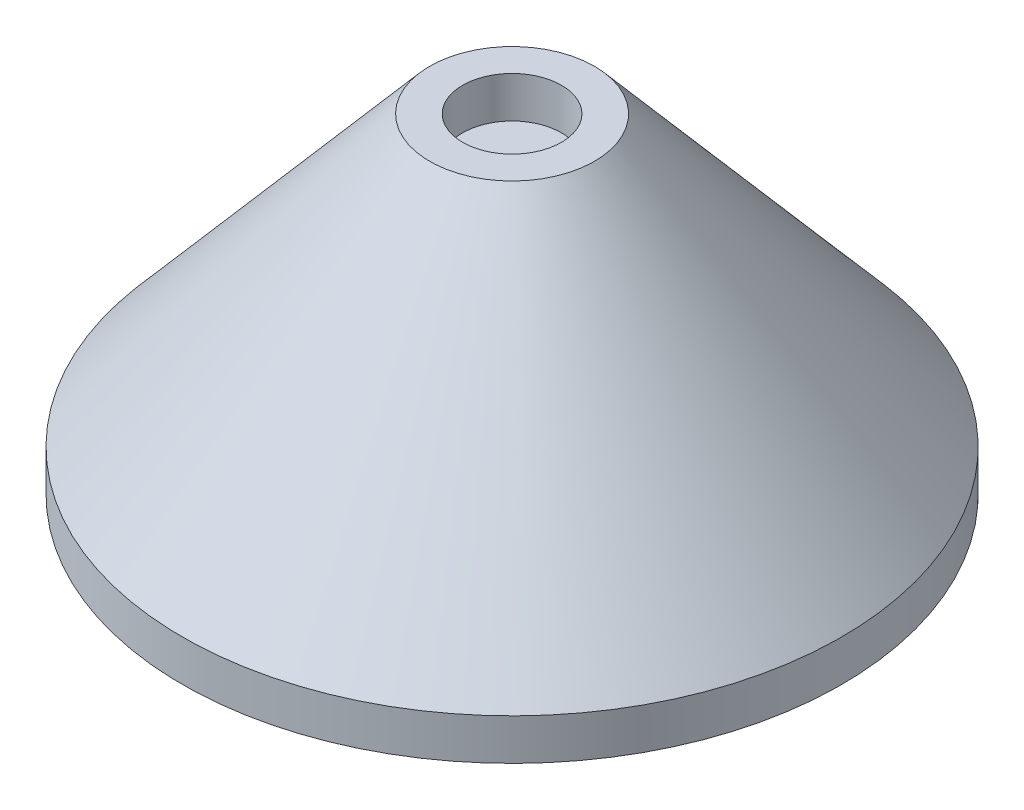
SolidWorks part; units mm, degrees
material "Nylon 101"
ref_plane "Front Plane" through (0, 0, 0) normal (0, 0, 1) x (1, 0, 0)
ref_plane "Top Plane" through (0, 0, 0) normal (0, 1, 0) x (1, 0, 0)
ref_plane "Right Plane" through (0, 0, 0) normal (1, 0, 0) x (0, 0, -1)
sketch "Sketch1" plane through (0, 0, 0) normal (0, 0, 1) x (1, 0, 0)
  line L0 (0, 0) -> (-10, 0)
  line L1 (-10, 0) -> (-40, -35)
  line L2 (-40, -35) -> (-40, -40)
  line L3 (-40, -40) -> (0, -40)
  line L4 (0, -40) -> (0, 0)
  dimension "D1" = 40
  dimension "D2" = 10
  dimension "D3" = 5
  dimension "D4" = 40
revolve "Revolve1" add sketch "Sketch1" angle 360 about L4
sketch "Sketch2" plane through (0, 0, 0) normal (0, 1, 0) x (1, 0, 0)
  circle A0 centre (0, 0) radius 6
  dimension "D1" = 12
extrude "Cut-Extrude1" cut sketch "Sketch2" against normal blind 5
